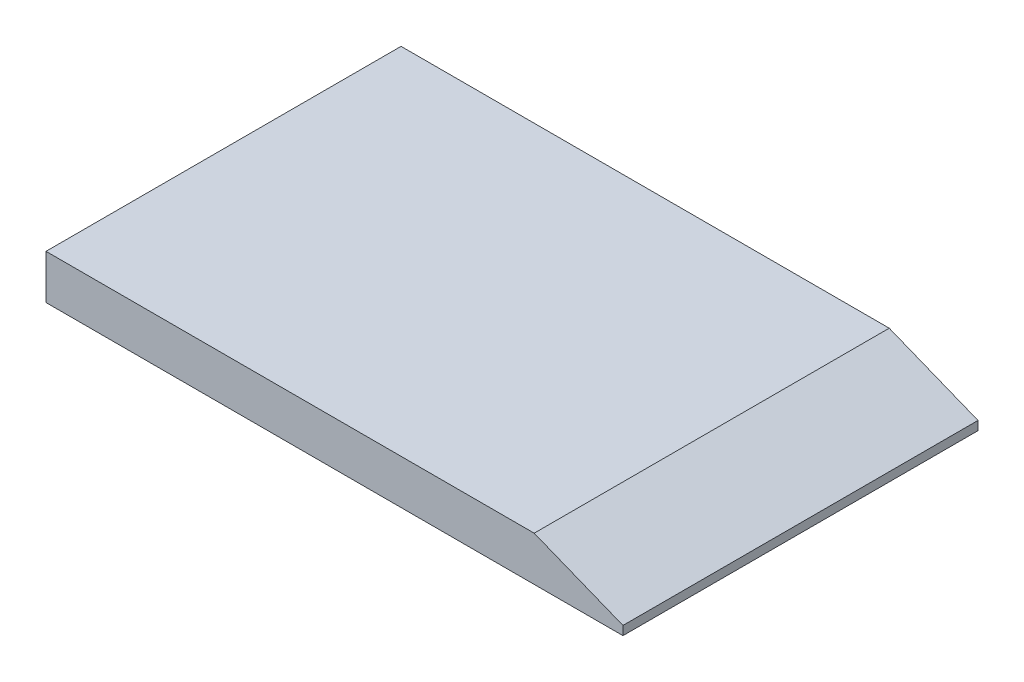
SolidWorks part; units mm, degrees
ref_plane "Front Plane" through (0, 0, 0) normal (0, 0, 1) x (1, 0, 0)
ref_plane "Top Plane" through (0, 0, 0) normal (0, 1, 0) x (1, 0, 0)
ref_plane "Right Plane" through (0, 0, 0) normal (1, 0, 0) x (0, 0, -1)
sketch "Sketch1" plane through (0, 0, 0) normal (0, 1, 0) x (1, 0, 0)
  line L1 (-65, -40) -> (65, -40)
  line L2 (-65, -40) -> (-65, 40)
  line L3 (-65, 40) -> (65, 40)
  line L4 (65, -40) -> (65, 40)
  line L5 (-65, -40) -> (65, 40) construction
  line L6 (-65, 40) -> (65, -40) construction
  point P0 (0, 0)
  dimension "D1" = 80
  dimension "D2" = 130
extrude "Boss-Extrude1" add sketch "Sketch1" along normal blind 10
sketch "Sketch2" plane through (0, 0, 40) normal (0, 0, 1) x (1, 0, 0)
  line L5 (65, 2) -> (45, 10)
  line L6 (65, 10) -> (65, 0) construction
  line L7 (-65, 10) -> (65, 10) construction
  line L8 (45, 10) -> (65, 10)
  line L9 (65, 10) -> (65, 2)
  line L10 (-65, 0) -> (65, 0) construction
  dimension "D1" = 2
  dimension "D2" = 20
extrude "Cut-Extrude1" cut sketch "Sketch2" against normal through all
